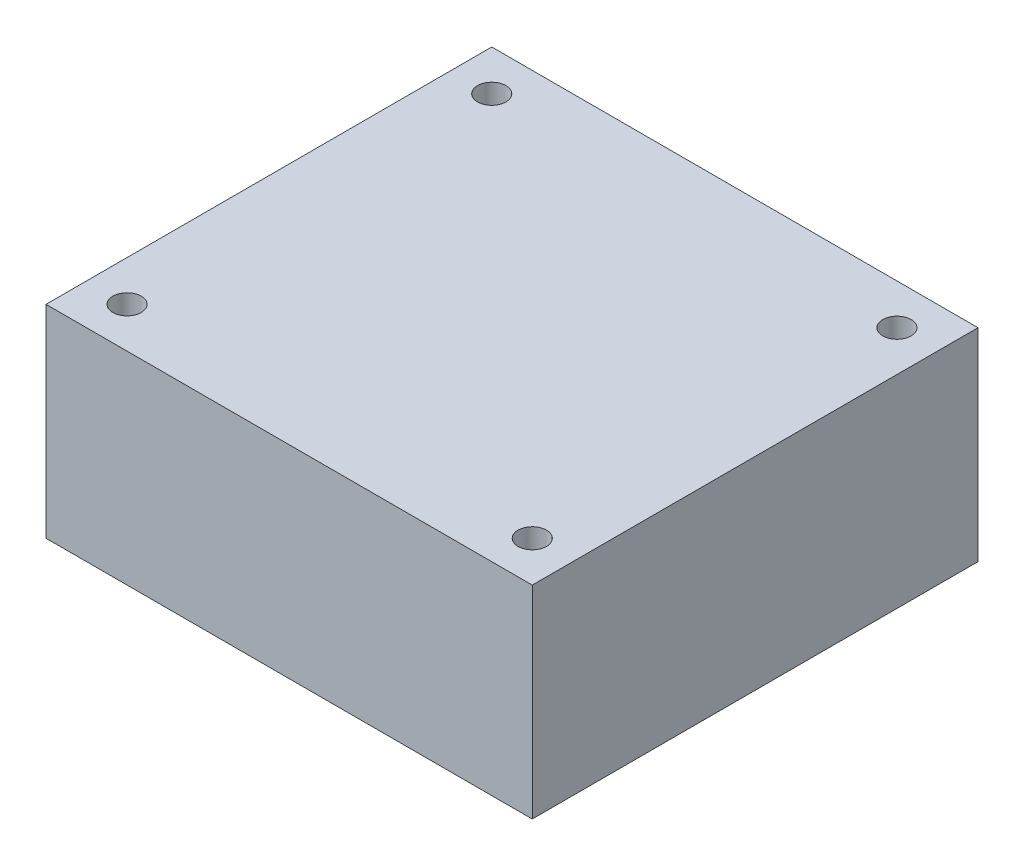
SolidWorks part; units mm, degrees
ref_plane "Płaszczyzna przednia" through (0, 0, 0) normal (0, 0, 1) x (1, 0, 0)
ref_plane "Płaszczyzna górna" through (0, 0, 0) normal (0, 1, 0) x (1, 0, 0)
ref_plane "Płaszczyzna prawa" through (0, 0, 0) normal (1, 0, 0) x (0, 0, -1)
sketch "Sketch1" plane through (0, 0, 0) normal (0, 1, 0) x (1, 0, 0)
  line L1 (-38, -38.726) -> (22, -38.726)
  line L2 (-38, -38.726) -> (-38, 16.274)
  line L3 (-38, 16.274) -> (22, 16.274)
  line L4 (22, -38.726) -> (22, 16.274)
  dimension "D1" = 60
  dimension "D2" = 55
extrude "Boss-Extrude1" add sketch "Sketch1" along normal blind 25
sketch "Sketch2" plane through (0, 25, 0) normal (0, 1, 0) x (1, 0, 0)
  line L0 (22, -38.726) -> (22, 16.274) construction
  line L1 (-33, 11.274) -> (17, 11.274) construction
  line L2 (-33, 11.274) -> (-33, -33.726) construction
  line L3 (-33, -33.726) -> (17, -33.726) construction
  line L4 (17, 11.274) -> (17, -33.726) construction
  line L5 (-38, -38.726) -> (22, -38.726) construction
  line L6 (-38, 16.274) -> (-38, -38.726) construction
  line L7 (22, 16.274) -> (-38, 16.274) construction
  circle A4 centre (-33, 11.274) radius 1.75
  circle A5 centre (17, 11.274) radius 1.75
  circle A6 centre (17, -33.726) radius 1.75
  circle A7 centre (-33, -33.726) radius 1.75
  dimension "D1" = 50
  dimension "D2" = 45
  dimension "D3" = 5
  dimension "D4" = 5
  dimension "D5" = 5
  dimension "D6" = 5
extrude "Cut-Extrude1" cut sketch "Sketch2" against normal through all
